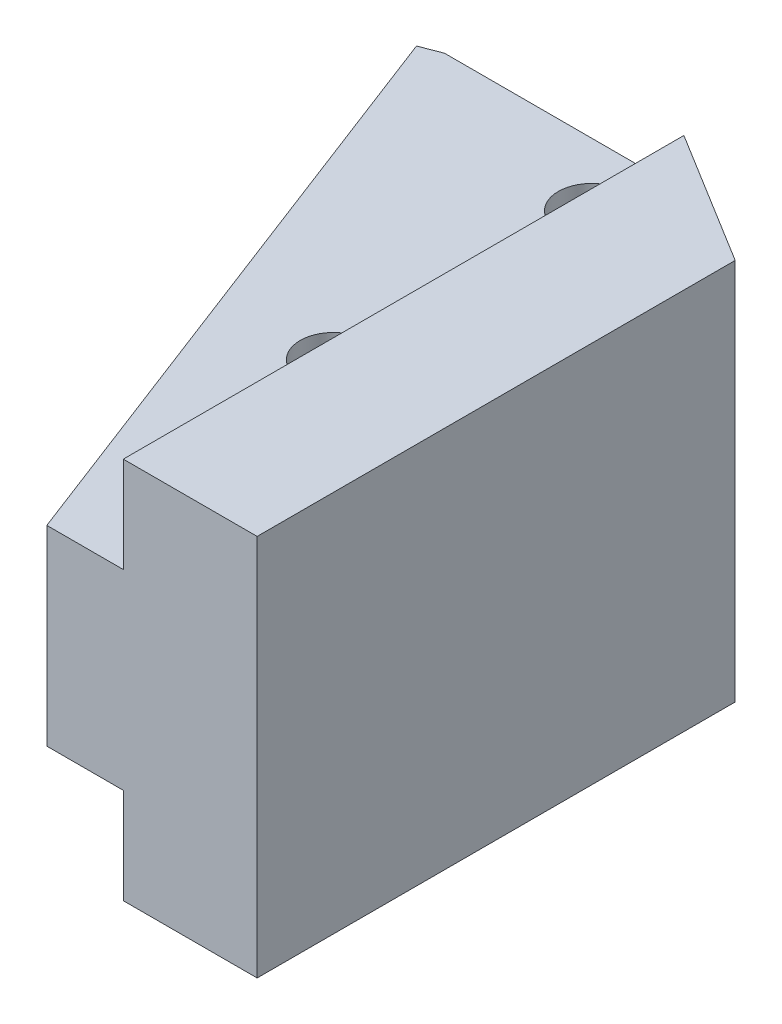
SolidWorks part; units mm, degrees
material "Gummi"
ref_plane "Ebene vorne" through (0, 0, 0) normal (0, 0, 1) x (1, 0, 0)
ref_plane "Ebene oben" through (0, 0, 0) normal (0, 1, 0) x (1, 0, 0)
ref_plane "Ebene rechts" through (0, 0, 0) normal (1, 0, 0) x (0, 0, -1)
sketch "Skizze1" plane through (0, 0, 0) normal (0, 0, 1) x (1, 0, 0)
  line L0 (0, 5) -> (0, -5)
  line L1 (0, -5) -> (4, -5)
  line L2 (4, -5) -> (4, -10)
  line L3 (4, -10) -> (11, -10)
  line L4 (11, -10) -> (11, 10)
  line L5 (11, 10) -> (4, 10)
  line L6 (4, 10) -> (4, 5)
  line L7 (4, 5) -> (0, 5)
  line L8 (0, 0) -> (27.3492, 0) construction
  dimension "D1" = 10
  dimension "D2" = 4
  dimension "D3" = 7
  dimension "D4" = 20
extrude "Aufsatz-Linear austragen1" add sketch "Skizze1" along normal blind 40
sketch "Skizze2" plane through (0, 5, 0) normal (0, 1, 0) x (1, 0, 0)
  line L0 (0, -40) -> (-12.0444, -8.6234)
  line L1 (-12.0444, -8.6234) -> (0, -4)
  line L2 (0, -40) -> (0, 0) construction
  line L3 (0, -4) -> (0, -40)
  line L4 (4, -40) -> (4, 0) construction
  dimension "D1" = 36
  dimension "D2" = 21
extrude "Aufsatz-Linear austragen2" add sketch "Skizze2" against normal up to surface (10 mm away) up to face at (2, -5, 20)
sketch "Skizze4" plane through (0, 10, 0) normal (0, 1, 0) x (1, 0, 0)
  line L0 (-10.9852, -8.2168) -> (0, -8.2168)
  line L1 (0, -4) -> (-12.0444, -8.6234) construction
  line L2 (0, -8.2168) -> (11, -15)
  line L3 (11, -40) -> (11, 0) construction
  line L4 (-10.9852, -8.2168) -> (0, -4)
  line L5 (0, -4) -> (0, 0)
  line L6 (0, 0) -> (11, 0)
  line L7 (11, 0) -> (11, -15)
  dimension "D1" = 15
extrude "Schnitt-Linear austragen1" cut sketch "Skizze4" against normal up to surface (20 mm away) up to face at (7.5, -10, 20)
sketch "Skizze5" plane through (0, 10, 0) normal (0, 1, 0) x (1, 0, 0)
  line L0 (11, -40) -> (4, -40) construction
  line L1 (4, -40) -> (4, -10.6834) construction
  line L2 (4, -40) -> (0, -40) construction
  circle A0 centre (0, -25) radius 1.75
  circle A1 centre (0, -11.5) radius 1.75
  dimension "D1" = 3.5
  dimension "D3" = 3.5
  dimension "D2" = 15
  dimension "D4" = 4
  dimension "D5" = 4
  dimension "D6" = 28.5
extrude "Schnitt-Linear austragen2" cut sketch "Skizze5" against normal through all both and the other way through all
sketch "Skizze6" plane through (11, 0, 0) normal (1, 0, 0) x (0, 0, -1)
  line L0 (-40, 10) -> (-15, 10) construction
  line L1 (-39, 10) -> (-37, 10)
  line L2 (-39, 10) -> (-39, -10)
  line L3 (-39, -10) -> (-37, -10)
  line L4 (-37, 10) -> (-37, -10)
  line L5 (-40, -10) -> (-15, -10) construction
  line L6 (-40, -10) -> (-40, 10) construction
  line L7 (-36, 10) -> (-34, 10)
  line L8 (-36, 10) -> (-36, -10)
  line L9 (-36, -10) -> (-34, -10)
  line L10 (-34, 10) -> (-34, -10)
  line L11 (-33, 10) -> (-31, 10)
  line L12 (-33, 10) -> (-33, -10)
  line L13 (-33, -10) -> (-31, -10)
  line L14 (-31, 10) -> (-31, -10)
  line L15 (-30, 10) -> (-28, 10)
  line L16 (-30, 10) -> (-30, -10)
  line L17 (-30, -10) -> (-28, -10)
  line L18 (-28, 10) -> (-28, -10)
  line L19 (-27, 10) -> (-25, 10)
  line L20 (-27, 10) -> (-27, -10)
  line L21 (-27, -10) -> (-25, -10)
  line L22 (-25, 10) -> (-25, -10)
  line L23 (-24, 10) -> (-22, 10)
  line L24 (-24, 10) -> (-24, -10)
  line L25 (-24, -10) -> (-22, -10)
  line L26 (-22, 10) -> (-22, -10)
  line L27 (-21, 10) -> (-19, 10)
  line L28 (-21, 10) -> (-21, -10)
  line L29 (-21, -10) -> (-19, -10)
  line L30 (-19, 10) -> (-19, -10)
  line L31 (-18, 10) -> (-16, 10)
  line L32 (-18, 10) -> (-18, -10)
  line L33 (-18, -10) -> (-16, -10)
  line L34 (-16, 10) -> (-16, -10)
  dimension "D1" = 1
  dimension "D2" = 2
  dimension "D3" = 8
extrude "Schnitt-Linear austragen3" [suppressed] cut sketch "Skizze6" against normal blind 1
sketch "Skizze7" plane through (11, 0, 0) normal (1, 0, 0) x (0, 0, -1)
  line L0 (-40, -10) -> (-40, 10) construction
  line L1 (-40, 9) -> (-10.6834, 9)
  line L2 (-40, 9) -> (-40, 7)
  line L3 (-40, 7) -> (-10.6834, 7)
  line L4 (-10.6834, 9) -> (-10.6834, 7)
  line L6 (-10.6834, 10) -> (-15, 10) construction
  line L7 (-10.6834, 10) -> (-10.6834, 5) construction
  line L8 (-40, 6) -> (-10.6834, 6)
  line L9 (-40, 6) -> (-40, 4)
  line L10 (-40, 4) -> (-10.6834, 4)
  line L11 (-10.6834, 6) -> (-10.6834, 4)
  line L12 (-40, 3) -> (-10.6834, 3)
  line L13 (-40, 3) -> (-40, 1)
  line L14 (-40, 1) -> (-10.6834, 1)
  line L15 (-10.6834, 3) -> (-10.6834, 1)
  line L16 (-40, 0) -> (-10.6834, 0)
  line L17 (-40, 0) -> (-40, -2)
  line L18 (-40, -2) -> (-10.6834, -2)
  line L19 (-10.6834, 0) -> (-10.6834, -2)
  line L20 (-40, -3) -> (-10.6834, -3)
  line L21 (-40, -3) -> (-40, -5)
  line L22 (-40, -5) -> (-10.6834, -5)
  line L23 (-10.6834, -3) -> (-10.6834, -5)
  line L24 (-40, -6) -> (-10.6834, -6)
  line L25 (-40, -6) -> (-40, -8)
  line L26 (-40, -8) -> (-10.6834, -8)
  line L27 (-10.6834, -6) -> (-10.6834, -8)
  point P10 (-12.8417, 10)
  dimension "D1" = 1
  dimension "D2" = 2
  dimension "D3" = 6
extrude "Schnitt-Linear austragen4" [suppressed] cut sketch "Skizze7" against normal blind 1
